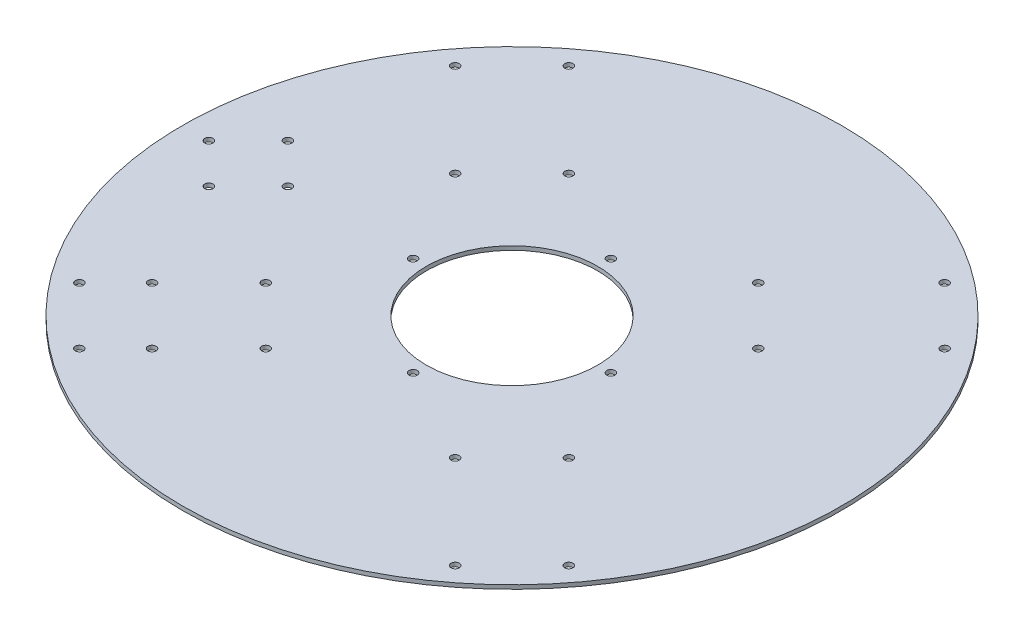
SolidWorks part; units mm, degrees
ref_plane "Front Plane" through (0, 0, 0) normal (0, 0, 1) x (1, 0, 0)
ref_plane "Top Plane" through (0, 0, 0) normal (0, 1, 0) x (1, 0, 0)
ref_plane "Right Plane" through (0, 0, 0) normal (1, 0, 0) x (0, 0, -1)
sketch "Sketch1" plane through (0, 0, 0) normal (0, 1, 0) x (1, 0, 0)
  circle A0 centre (0, 0) radius 32.5
  circle A1 centre (0, 0) radius 125
  circle A2 centre (-37.5, 0) radius 1.55
  circle A3 centre (-37.5, 0) radius 1.55
  circle A4 centre (37.5, 0) radius 1.55
  circle A5 centre (37.5, 0) radius 1.55
  circle A6 centre (0, 37.5) radius 1.55
  circle A7 centre (0, -37.5) radius 1.55
  dimension "D1" = 65
  dimension "D2" = 250
  dimension "D3" = 3.1
  dimension "D4" = 3.1
  dimension "D5" = 3.1
  dimension "D6" = 3.1
  dimension "D7" = 75
  dimension "D8" = 37.5
  dimension "D9" = 75
  dimension "D10" = 37.5
  dimension "D11" = 3.1
  dimension "D12" = 3.1
  dimension "D13" = 75
  dimension "D14" = 37.5
extrude "Boss-Extrude1" add sketch "Sketch1" along normal blind 1.5 contours A1 A7 A6 A4 A2 A0
sketch "Sketch2" plane through (0, 1.5, 0) normal (0, 1, 0) x (1, 0, 0)
  line L0 (-92.8358, 71.2691) -> (-71.2691, 92.8358) construction
  line L1 (0, 0) -> (0, 125) construction
  line L2 (0, 0) -> (-125, 0) construction
  line L3 (-92.8358, 71.2691) -> (-21.5667, 0) construction
  line L4 (-57.4805, 35.9137) -> (-35.9137, 57.4805) construction
  line L5 (-71.2691, 92.8358) -> (0, 21.5668) construction
  line L6 (-92.8358, 71.2691) -> (-98.5115, 76.9447) construction
  line L7 (-35.9137, -57.4805) -> (-71.2691, -92.8358) construction
  line L8 (-71.2691, -92.8358) -> (-92.8358, -71.2691) construction
  line L9 (-92.8358, -71.2691) -> (-57.4805, -35.9137) construction
  line L10 (-57.4805, -79.0472) -> (-79.0472, -57.4805) construction
  circle A0 centre (-71.2691, 92.8358) radius 1.55
  circle A1 centre (-35.9137, 57.4805) radius 1.55
  circle A2 centre (-92.8358, 71.2691) radius 1.55
  circle A3 centre (-57.4805, 35.9137) radius 1.55
  circle A4 centre (0, 0) radius 125 construction
  circle A5 centre (71.2691, 92.8358) radius 1.55
  circle A6 centre (92.8358, 71.2691) radius 1.55
  circle A7 centre (35.9137, 57.4805) radius 1.55
  circle A8 centre (57.4805, 35.9137) radius 1.55
  circle A9 centre (92.8358, -71.2691) radius 1.55
  circle A10 centre (71.2691, -92.8358) radius 1.55
  circle A11 centre (57.4805, -35.9137) radius 1.55
  circle A12 centre (35.9137, -57.4805) radius 1.55
  circle A13 centre (-71.2691, -92.8358) radius 1.55
  circle A14 centre (-92.8358, -71.2691) radius 1.55
  circle A15 centre (-35.9137, -57.4805) radius 1.55
  circle A16 centre (-57.4805, -35.9137) radius 1.55
  circle A19 centre (-57.4805, -79.0472) radius 1.55
  circle A20 centre (-79.0472, -57.4805) radius 1.55
  point P45 (0, 0)
  point P47 (-54.9417, -85.68)
  point P48 (-51.494, -73.0608)
  dimension "D1" = 3.1
  dimension "D2" = 3.1
  dimension "D3" = 3.1
  dimension "D4" = 3.1
  dimension "D9" = 30.5
  dimension "D10" = 90
  dimension "D11" = 50
  dimension "D15" = 30.5
  dimension "D18" = 3.1
  dimension "D19" = 3.1
  dimension "D14" = 30.5
  dimension "D5" = 135
  dimension "D6" = 45
  dimension "D7" = 135
  dimension "D8" = 30.5
  dimension "D12" = 8.0266
  dimension "D13" = 4
extrude "Cut-Extrude1" cut sketch "Sketch2" against normal up to surface (1.5 mm away) up to face at (0, 0, 39.05)
sketch "Sketch3" plane through (0, 1.5, 0) normal (0, 1, 0) x (1, 0, 0)
  circle A0 centre (-100, 15) radius 1.55
  circle A1 centre (-100, -15) radius 1.55
  circle A2 centre (-85, 0) radius 1.55
  circle A3 centre (-115, 0) radius 1.55
  dimension "D1" = 3.1
  dimension "D2" = 3.1
  dimension "D3" = 3.1
  dimension "D4" = 3.1
  dimension "D5" = 15
  dimension "D6" = 15
  dimension "D7" = 30
  dimension "D8" = 30
  dimension "D9" = 85
extrude "Cut-Extrude2" cut sketch "Sketch3" against normal up to surface (1.5 mm away) up to face at (-92.8358, 0, 72.8191)
